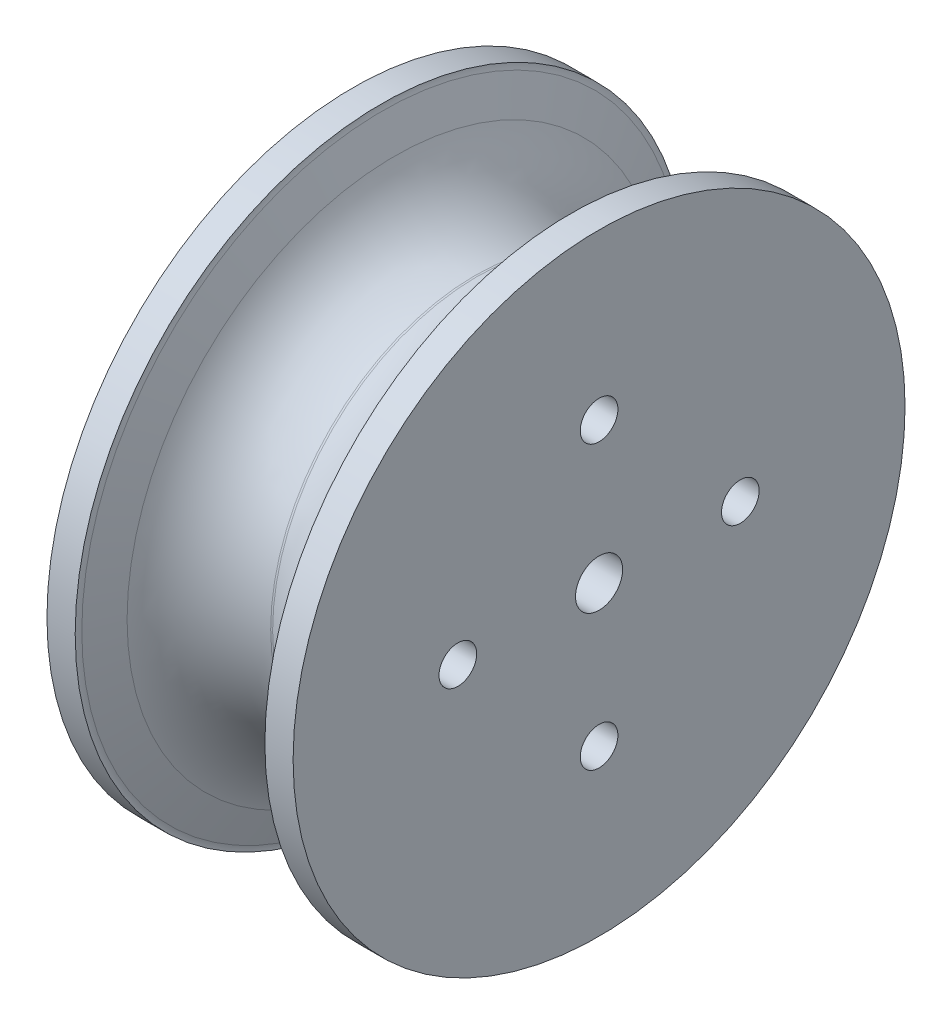
SolidWorks part; units mm, degrees
ref_plane "Front Plane" through (0, 0, 0) normal (0, 0, 1) x (1, 0, 0)
ref_plane "Top Plane" through (0, 0, 0) normal (0, 1, 0) x (1, 0, 0)
ref_plane "Right Plane" through (0, 0, 0) normal (1, 0, 0) x (0, 0, -1)
sketch "Sketch1" plane through (0, 0, 0) normal (0, 0, 1) x (1, 0, 0)
  line L0 (-10.0737, 51.1001) -> (-10.0737, 21.1001)
  line L1 (-10.0737, 51.1001) -> (-13.0737, 51.1001)
  line L2 (-10.0737, 21.1001) -> (-13.0737, 21.1001)
  line L3 (-13.0737, 51.1001) -> (-13.0737, 21.1001)
  line L4 (-9.9654, 21.6934) -> (-8.6466, 25.1843)
  line L8 (0, 51.1001) -> (0, 21.1001) construction
  line L9 (-10.0737, 21.1001) -> (-10.0737, 51.1001)
  line L11 (9.9654, 21.6934) -> (8.6466, 25.1843)
  line L14 (10.0737, 21.1001) -> (13.0737, 21.1001)
  line L15 (-10.0737, 51.1001) -> (10.0737, 51.1001)
  line L16 (10.0737, 51.1001) -> (10.0737, 21.1001)
  line L17 (-31.3431, 53.6001) -> (30.8573, 53.6001) construction
  line L18 (13.0737, 51.1001) -> (13.0737, 21.1001)
  line L19 (10.0737, 51.1001) -> (13.0737, 51.1001)
  line L20 (10.0737, 51.1001) -> (10.0737, 21.1001)
  arc A4 (-0.102, 31.8938) -> (-8.6466, 25.1843) centre (1.173, 21.4746) ccw
  arc A5 (-9.9654, 21.6934) -> (-10.0737, 21.1001) centre (-8.3948, 21.1001) ccw
  arc A7 (0.102, 31.8938) -> (-0.102, 31.8938) centre (0, 31.0606) ccw
  arc A8 (9.9654, 21.6934) -> (10.0737, 21.1001) centre (8.3948, 21.1001) cw
  arc A9 (0.102, 31.8938) -> (8.6466, 25.1843) centre (-1.173, 21.4746) cw
  dimension "D1" = 2.5
  dimension "D2" = 30
  dimension "D3" = 3
revolve "Revolve1" add sketch "Sketch1" angle 360 about L17
sketch "Sketch2" plane through (-13.0737, 0, 0) normal (-1, 0, 0) x (0, 0, 1)
  circle A0 centre (0, 53.6001) radius 15 construction
  circle A1 centre (0, 68.6001) radius 2
  circle A2 centre (15, 53.6001) radius 2
  circle A3 centre (0, 38.6001) radius 2
  circle A4 centre (-15, 53.6001) radius 2
  point P14 (0, 53.6001)
  dimension "D1" = 30
  dimension "D2" = 4
  dimension "D3" = 4
extrude "Cut-Extrude1" cut sketch "Sketch2" against normal blind 31
